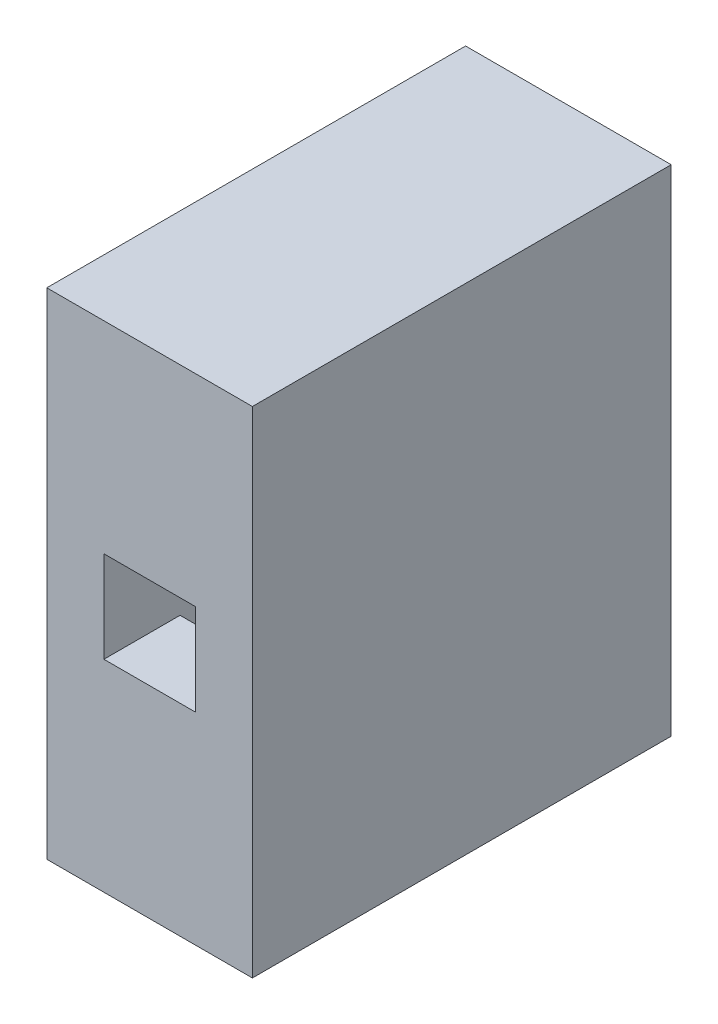
SolidWorks part; units mm, degrees
ref_plane "Front Plane" through (0, 0, 0) normal (0, 0, 1) x (1, 0, 0)
ref_plane "Top Plane" through (0, 0, 0) normal (0, 1, 0) x (1, 0, 0)
ref_plane "Right Plane" through (0, 0, 0) normal (1, 0, 0) x (0, 0, -1)
sketch "Sketch1" plane through (0, 0, 0) normal (0, 0, 1) x (1, 0, 0)
  line L1 (-2.4, -10) -> (2.4, -10)
  line L2 (-2.4, -10) -> (-2.4, 10)
  line L3 (-2.4, 10) -> (2.4, 10)
  line L4 (2.4, -10) -> (2.4, 10)
  line L5 (-2.4, -10) -> (2.4, 10) construction
  line L6 (-2.4, 10) -> (2.4, -10) construction
  line L7 (-5.4, -13) -> (5.4, -13)
  line L8 (-5.4, -13) -> (-5.4, 13)
  line L9 (-5.4, 13) -> (5.4, 13)
  line L10 (5.4, -13) -> (5.4, 13)
  line L11 (-5.4, -13) -> (5.4, 13) construction
  line L12 (-5.4, 13) -> (5.4, -13) construction
  line L13 (-2.4, 2.4) -> (2.4, 2.4)
  line L14 (-2.4, 2.4) -> (-2.4, -2.4)
  line L15 (-2.4, -2.4) -> (2.4, -2.4)
  line L16 (2.4, 2.4) -> (2.4, -2.4)
  line L17 (-2.4, 2.4) -> (2.4, -2.4) construction
  line L18 (-2.4, -2.4) -> (2.4, 2.4) construction
  point P0 (0, 0)
  point P6 (0, 0)
  point P11 (0, 0)
  dimension "D1" = 4.8
  dimension "D2" = 20
  dimension "D3" = 26
  dimension "D4" = 10.8
  dimension "D5" = 4.8
extrude "Boss-Extrude1" add sketch "Sketch1" along normal blind 18 contours L7 L10 L9 L8 L4 L1 L2 L3
sketch "Sketch2" plane through (0, 0, 18) normal (0, 0, 1) x (1, 0, 0)
  line L0 (2.4, -10) -> (2.4, 10) construction
  line L1 (-2.4, 2.4) -> (2.4, 2.4)
  line L2 (-2.4, 2.4) -> (-2.4, -2.4)
  line L3 (-2.4, -2.4) -> (2.4, -2.4)
  line L4 (2.4, 2.4) -> (2.4, -2.4)
  line L5 (-2.4, 2.4) -> (2.4, -2.4) construction
  line L6 (-2.4, -2.4) -> (2.4, 2.4) construction
  line L8 (-5.4, -13) -> (5.4, -13)
  line L9 (-5.4, -13) -> (-5.4, 13)
  line L10 (-5.4, 13) -> (5.4, 13)
  line L11 (5.4, -13) -> (5.4, 13)
  line L12 (-5.4, -13) -> (5.4, 13) construction
  line L13 (-5.4, 13) -> (5.4, -13) construction
  point P1 (0, 0)
  point P8 (0, 0)
  dimension "D1" = 4.8
extrude "Boss-Extrude2" add sketch "Sketch2" along normal blind 4
